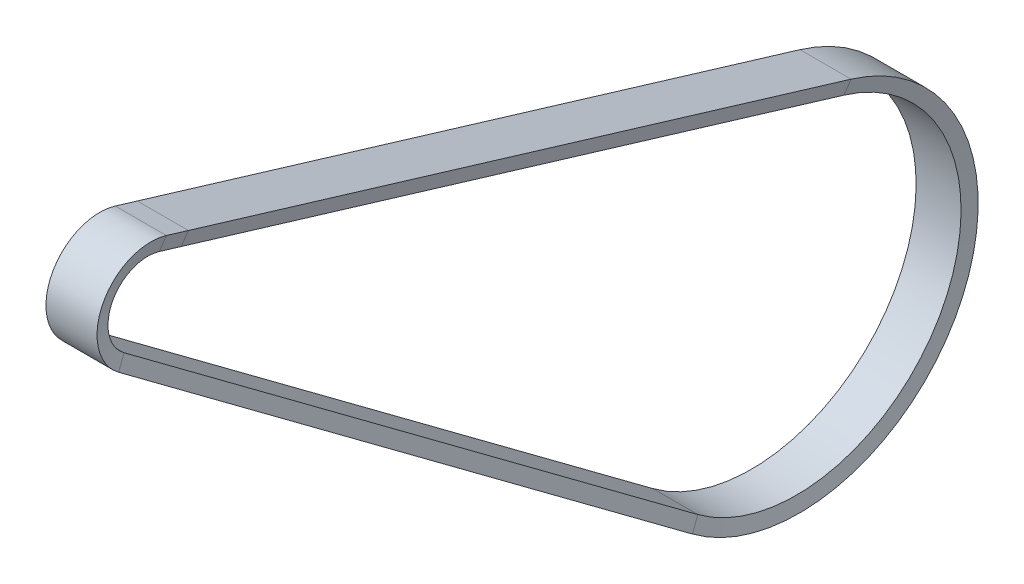
SolidWorks part; units mm, degrees
ref_plane "Piano frontale" through (0, 0, 0) normal (0, 0, 1) x (1, 0, 0)
ref_plane "Piano superiore" through (0, 0, 0) normal (0, 1, 0) x (1, 0, 0)
ref_plane "Piano destro" through (0, 0, 0) normal (1, 0, 0) x (0, 0, -1)
sketch "Schizzo2" plane through (0, 0, 0) normal (1, 0, 0) x (0, 0, -1)
  line L0 (13.1455, 85.4936) -> (267.7362, 8.5535)
  line L1 (213.3983, -99.3164) -> (0.0356, 59.4682)
  line L3 (8.8664, 71.3345) -> (250.0004, -50.1332) construction
  arc A2 (13.1455, 85.4936) -> (0.0356, 59.4682) centre (8.8664, 71.3345) ccw
  arc A3 (213.3983, -99.3164) -> (267.7362, 8.5535) centre (250.0004, -50.1332) ccw
  circle A4 centre (8.8664, 71.3345) radius 10 construction
  circle A5 centre (250.0004, -50.1332) radius 31.5795 construction
  dimension "D1" = 787.1085
sketch "Schizzo1" plane through (0, 0, 0) normal (0, 0, 1) x (1, 0, 0)
  line L0 (-9.5, -23.292) -> (9.5, -23.292)
  line L4 (-9.5, -23.292) -> (-8.3566, -28.4926)
  line L6 (9.5, -23.292) -> (8.3566, -28.4926)
  line L7 (-8.3566, -28.4926) -> (8.3566, -28.4926)
  line L8 (0, -23.292) -> (0, -28.4926) construction
  line L11 (0, 85.4936) -> (0, 8.5535) construction
  point P2 (0, -23.292)
  point P4 (0, -25.8923)
  dimension "D1" = 16.7131
  dimension "D2" = 24.8
  dimension "D3" = 5.2006
  dimension "D4" = 12.4
  dimension "D5" = 19
sketch3d "Schizzo3D1"
  line L0 (9.5003, 88.0024, -22.8457) -> (-9.4997, 88.0024, -22.8457)
  line L1 (-9.4997, 88.0024, -22.8457) -> (-8.355, 83.0174, -21.3391)
  line L2 (-8.355, 83.0174, -21.3391) -> (8.355, 83.0174, -21.3391)
  line L3 (8.355, 83.0174, -21.3391) -> (9.5003, 88.0024, -22.8457)
  line L4 (0, 88.0024, -22.8457) -> (0, 83.0174, -21.3391) construction
  line L5 (0, 85.4936, -13.1455) -> (0, 8.5531, -267.7361) construction
  dimension "D1" = 16.71
  dimension "D2" = 19
  dimension "D4" = 5.2078
  dimension "D3" = 24.8
sweep "Sweep2" add profiles "Schizzo3D1" path "Schizzo2"
ref_plane "Piano1" through (8.355, 83.0174, -21.3391) normal (1, 0, 0) x (0, 0, -1)
sketch "Schizzo3" plane through (8.355, 83.0174, -21.3391) normal (1, 0, 0) x (0, 0, -1)
  line L0 (192.0592, -182.3337) -> (-21.3035, -23.5491) construction
  line L1 (-8.1936, 2.4762) -> (246.3971, -74.4638) construction
  line L2 (192.0592, -182.3337) -> (-21.3035, -23.5491)
  line L3 (-8.1936, 2.4762) -> (246.3971, -74.4638)
  arc A0 (192.0592, -182.3337) -> (246.3971, -74.4638) centre (228.6613, -133.1506) ccw construction
  arc A1 (-8.1936, 2.4762) -> (-21.3035, -23.5491) centre (-12.4726, -11.6829) ccw construction
  arc A2 (192.0592, -182.3337) -> (246.3971, -74.4638) centre (228.6613, -133.1506) ccw
  arc A3 (-8.1936, 2.4762) -> (-21.3035, -23.5491) centre (-12.4726, -11.6829) ccw
ref_plane "Piano2" through (-8.355, 83.0174, -21.3391) normal (1, 0, 0) x (0, 0, -1)
sketch "Schizzo4" plane through (-8.355, 83.0174, -21.3391) normal (1, 0, 0) x (0, 0, -1)
  line L0 (192.0592, -182.3337) -> (-21.3035, -23.5491) construction
  line L1 (-8.1936, 2.4762) -> (246.3971, -74.4638) construction
  line L2 (192.0592, -182.3337) -> (-21.3035, -23.5491)
  line L3 (-8.1936, 2.4762) -> (246.3971, -74.4638)
  arc A0 (-8.1936, 2.4762) -> (-21.3035, -23.5491) centre (-12.4726, -11.6829) ccw construction
  arc A1 (192.0592, -182.3337) -> (246.3971, -74.4638) centre (228.6613, -133.1506) ccw construction
  arc A2 (-8.1936, 2.4762) -> (-21.3035, -23.5491) centre (-12.4726, -11.6829) ccw
  arc A3 (192.0592, -182.3337) -> (246.3971, -74.4638) centre (228.6613, -133.1506) ccw
